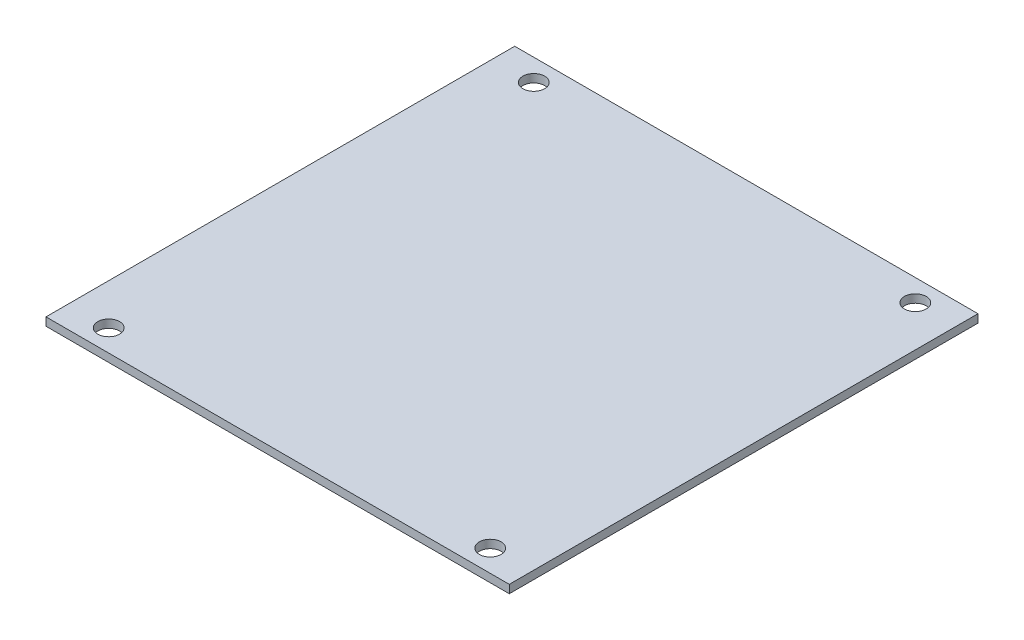
SolidWorks part; units mm, degrees
material "AISI 316 Stainless Steel Sheet (SS)"
ref_plane "Front Plane" through (0, 0, 0) normal (0, 0, 1) x (1, 0, 0)
ref_plane "Top Plane" through (0, 0, 0) normal (0, 1, 0) x (1, 0, 0)
ref_plane "Right Plane" through (0, 0, 0) normal (1, 0, 0) x (0, 0, -1)
sketch "Sketch1" plane through (0, 0, 0) normal (0, 1, 0) x (1, 0, 0)
  line L0 (0, -86) -> (0, 86) construction
  line L1 (-85, -86) -> (85, -86)
  line L2 (-85, -86) -> (-85, 86)
  line L3 (-85, 86) -> (85, 86)
  line L4 (85, -86) -> (85, 86)
  line L5 (-85, -86) -> (85, 86) construction
  line L6 (-85, 86) -> (85, -86) construction
  line L7 (-85, 0) -> (85, 0) construction
  circle A0 centre (-70, 78) radius 4
  circle A1 centre (70, 78) radius 4
  circle A2 centre (70, -78) radius 4
  circle A3 centre (-70, -78) radius 4
  point P0 (0, 0)
  dimension "D3" = 8
  dimension "D1" = 172
  dimension "D2" = 170
  dimension "D4" = 70
  dimension "D5" = 8
extrude "Boss-Extrude1" add sketch "Sketch1" along normal blind 3
